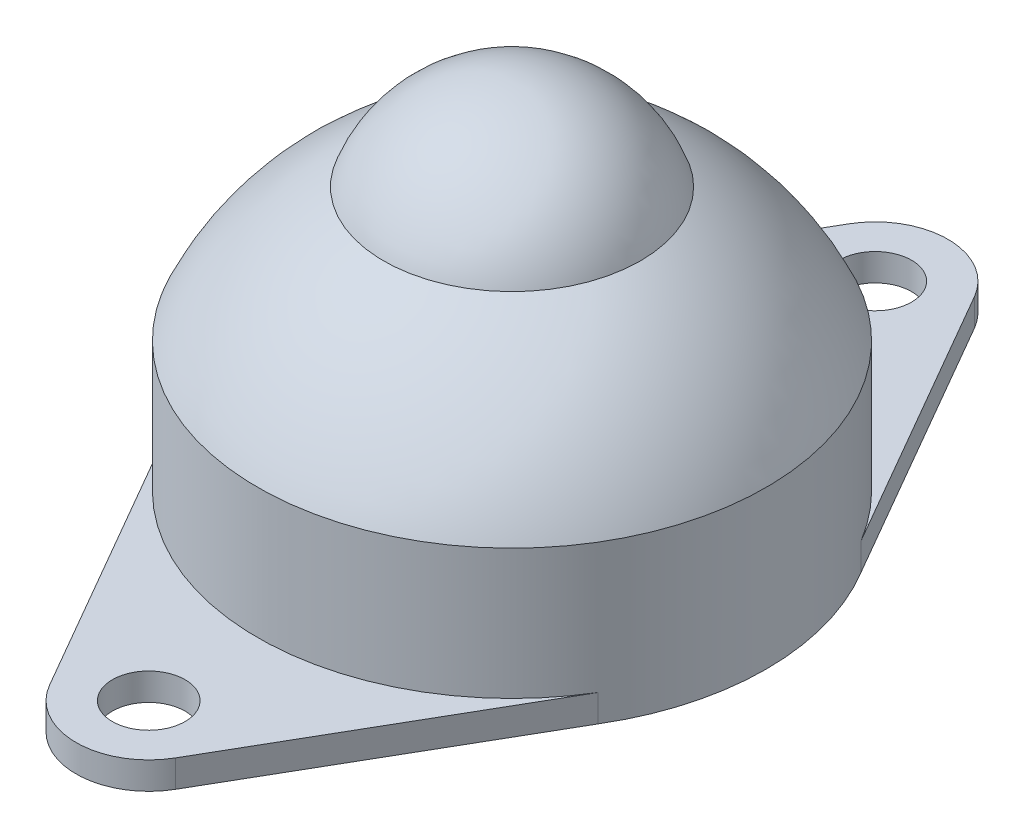
SolidWorks part; units mm, degrees
ref_plane "前视基准面" through (0, 0, 0) normal (0, 0, 1) x (1, 0, 0)
ref_plane "上视基准面" through (0, 0, 0) normal (0, 1, 0) x (1, 0, 0)
ref_plane "右视基准面" through (0, 0, 0) normal (1, 0, 0) x (0, 0, -1)
sketch "草图1" plane through (0, 0, 0) normal (0, 0, 1) x (1, 0, 0)
  line L0 (0, 0) -> (0, 31.1628) construction
  line L1 (0, 0) -> (-14, 0)
  line L2 (-14, 0) -> (-14, 8.6663)
  line L3 (0, 0) -> (0, 21)
  arc A2 (0, 21) -> (-7.0711, 16) centre (0, 13.5) ccw
  arc A3 (-7.0711, 16) -> (-14, 8.6663) centre (0, 2.3791) ccw
  point P9 (-7.0711, 16)
  dimension "D2" = 15
  dimension "D1" = 14
  dimension "D3" = 13.5
  dimension "D4" = 16
revolve "旋转1" add sketch "草图1" angle 360 about L0
sketch "草图2" plane through (0, 0, 0) normal (0, 1, 0) x (1, 0, 0)
  line L0 (0, 0) -> (0, 35.126) construction
  line L1 (3.4644, 21.9994) -> (11.9808, 7.2429)
  line L2 (14, 0) -> (-15.0932, 0) construction
  line L3 (-3.4644, 21.9994) -> (-11.9808, 7.2429)
  line L4 (-3.4644, -21.9994) -> (-11.9808, -7.2429)
  line L5 (3.4644, -21.9994) -> (11.9808, -7.2429)
  circle A0 centre (0, 0) radius 14 construction
  arc A2 (11.9808, -7.2429) -> (11.9808, 7.2429) centre (0, 0) ccw
  arc A3 (-11.9808, -7.2429) -> (-11.9808, 7.2429) centre (0, 0) cw
  arc A4 (3.4644, 21.9994) -> (-3.4644, 21.9994) centre (0, 20) ccw
  circle A5 centre (0, 20) radius 2
  circle A6 centre (0, -20) radius 2
  arc A7 (3.4644, -21.9994) -> (-3.4644, -21.9994) centre (0, -20) cw
  point P13 (0, 28.0023)
  dimension "D1" = 4
  dimension "D2" = 4
  dimension "D3" = 20
extrude "凸台-拉伸1" add sketch "草图2" along normal blind 1.5 contours L1 A2 L5 A7 L4 A3 L3 A4 | A5 | A6
